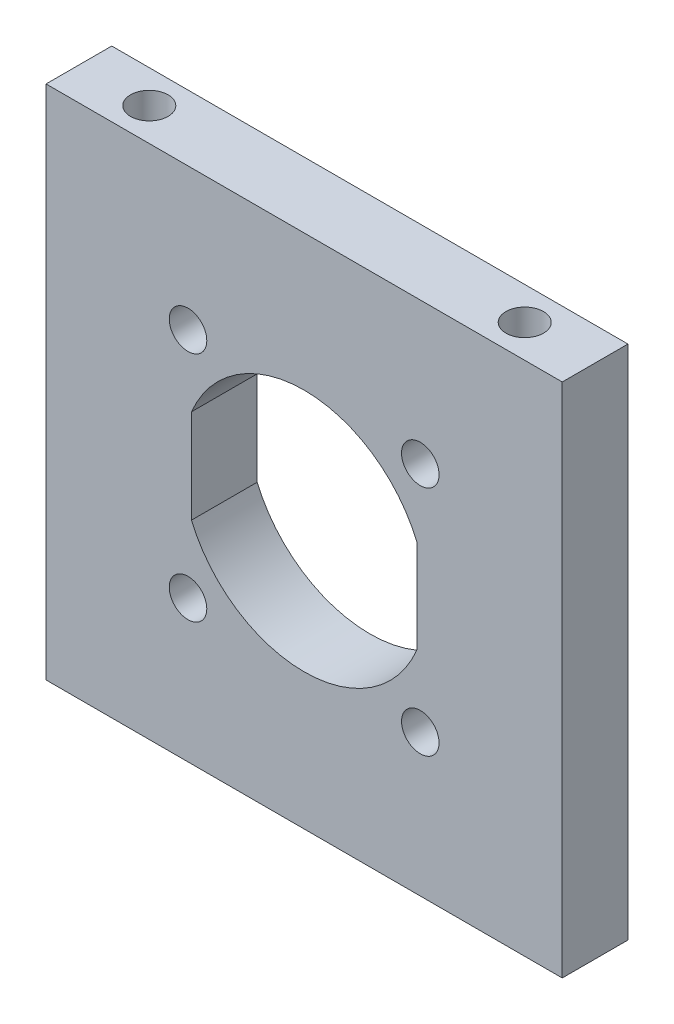
SolidWorks part; units mm, degrees
ref_plane "Front Plane" through (0, 0, 0) normal (0, 0, 1) x (1, 0, 0)
ref_plane "Top Plane" through (0, 0, 0) normal (0, 1, 0) x (1, 0, 0)
ref_plane "Right Plane" through (0, 0, 0) normal (1, 0, 0) x (0, 0, -1)
sketch "Sketch1" plane through (0, 0, 0) normal (0, 0, 1) x (1, 0, 0)
  line L0 (0, 18.7103) -> (0, -18.7103) construction
  line L1 (-27.5, 27.5) -> (27.5, 27.5)
  line L2 (-27.5, 27.5) -> (-27.5, -27.5)
  line L3 (-27.5, -27.5) -> (27.5, -27.5)
  line L4 (27.5, 27.5) -> (27.5, -27.5)
  line L5 (-27.5, 27.5) -> (27.5, -27.5) construction
  line L6 (-27.5, -27.5) -> (27.5, 27.5) construction
  line L7 (-15.0288, 15.0288) -> (15.0288, -15.0288) construction
  line L8 (12, 5) -> (12, -5)
  line L9 (-12, 5) -> (-12, -5)
  line L10 (12, 18.7103) -> (12, -18.7103) construction
  arc A0 (-12, -5) -> (12, -5) centre (0, 0) ccw
  arc A1 (12, 5) -> (-12, 5) centre (0, 0) ccw
  circle A2 centre (-12.3744, 12.3744) radius 2
  circle A3 centre (12.3744, 12.3744) radius 2
  circle A4 centre (12.3744, -12.3744) radius 2
  circle A5 centre (-12.3744, -12.3744) radius 2
  point P0 (0, 0)
  point P8 (-12, 18.7103)
  point P11 (0, 0)
  point P12 (-12, -18.7103)
  point P21 (0, 0)
  point P32 (0, 0)
  dimension "D3" = 26
  dimension "D7" = 4
  dimension "D1" = 55
  dimension "D2" = 55
  dimension "D4" = 12
  dimension "D6" = 10
  dimension "D8" = 17.5
  dimension "D9" = 45
  dimension "D5" = 12
  dimension "D10" = 4
extrude "Boss-Extrude1" add sketch "Sketch1" along normal blind 7
sketch "Sketch2" plane through (0, 27.5, 0) normal (0, 1, 0) x (1, 0, 0)
  line L0 (0, 0) -> (0, -7) construction
  line L1 (27.5, -7) -> (-27.5, -7) construction
  line L2 (27.5, 0) -> (-27.5, 0) construction
  circle A0 centre (-20, -3.5) radius 2
  circle A1 centre (20, -3.5) radius 2
  dimension "D1" = 4
  dimension "D2" = 3.5
  dimension "D3" = 20
extrude "Cut-Extrude1" cut sketch "Sketch2" against normal blind 9
sketch "Sketch3" plane through (0, -27.5, 0) normal (0, -1, 0) x (1, 0, 0)
  line L0 (0, 0) -> (0, 7) construction
  line L1 (-27.5, 7) -> (27.5, 7) construction
  circle A0 centre (-20, 3.5) radius 2
  circle A1 centre (20, 3.5) radius 2
  dimension "D1" = 4
  dimension "D2" = 20
  dimension "D3" = 3.5
extrude "Cut-Extrude2" cut sketch "Sketch3" against normal blind 9
